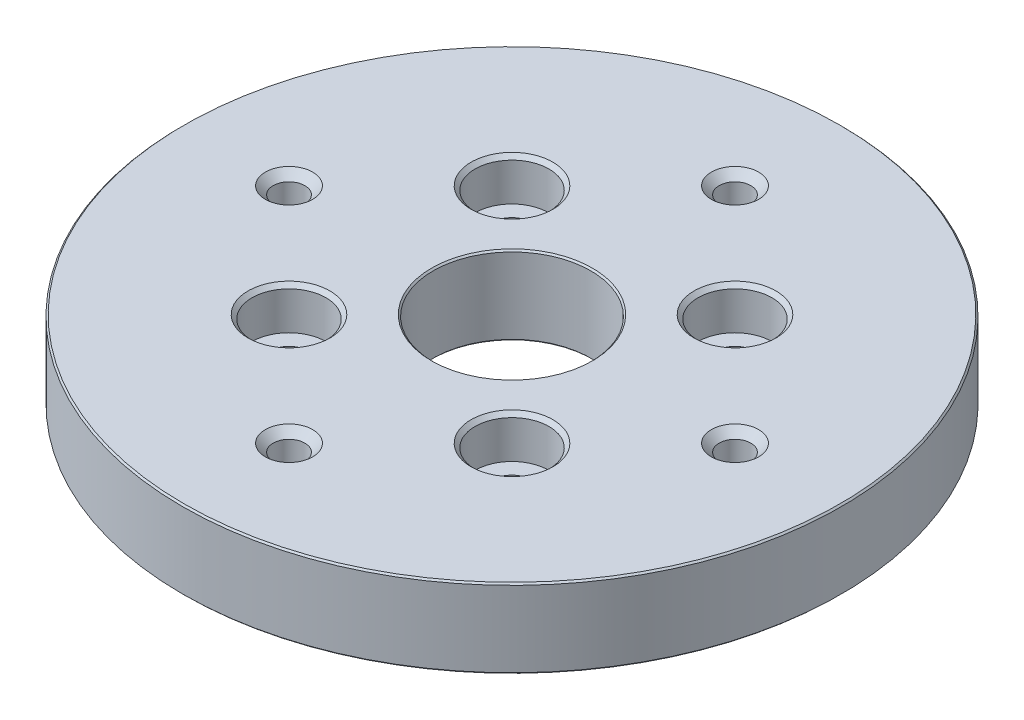
SolidWorks part; units mm, degrees
material "6061-T6 (SS)"
ref_plane "Front Plane" through (0, 0, 0) normal (0, 0, 1) x (1, 0, 0)
ref_plane "Top Plane" through (0, 0, 0) normal (0, 1, 0) x (1, 0, 0)
ref_plane "Right Plane" through (0, 0, 0) normal (1, 0, 0) x (0, 0, -1)
sketch "Sketch1" plane through (0, 0, 0) normal (0, 1, 0) x (1, 0, 0)
  line L0 (0, 35.921) -> (-35.921, 0) construction
  line L1 (-17.9605, 17.9605) -> (17.9605, 17.9605) construction
  line L2 (-17.9605, 17.9605) -> (-17.9605, -17.9605) construction
  line L3 (-17.9605, -17.9605) -> (17.9605, -17.9605) construction
  line L4 (17.9605, 17.9605) -> (17.9605, -17.9605) construction
  line L5 (-17.9605, 17.9605) -> (17.9605, -17.9605) construction
  line L6 (-17.9605, -17.9605) -> (17.9605, 17.9605) construction
  line L7 (0, 35.921) -> (35.921, 0) construction
  line L8 (-35.921, 0) -> (0, -35.921) construction
  line L9 (35.921, 0) -> (0, -35.921) construction
  line L10 (0, 35.921) -> (0, -35.921) construction
  line L11 (-35.921, 0) -> (35.921, 0) construction
  circle A0 centre (0, 0) radius 53.086
  circle A1 centre (0, 0) radius 12.7
  dimension "D1" = 106.172
  dimension "D2" = 25.4
  dimension "D3" = 50.8
  dimension "D4" = 50.8
extrude "Boss-Extrude1" add sketch "Sketch1" against normal blind 12.7
hole_wizard "1/4-20 Tapped Hole1" positions "Sketch3" profile "Sketch4" tap size "1/4-20" standard "ANSI Inch" end condition up to next
sketch "Sketch3" plane through (0, 0, 0) normal (0, 1, 0) x (1, 0, 0)
  point P0 (0, -35.921)
  point P3 (-35.921, 0)
  point P6 (0, 35.921)
  point P9 (35.921, 0)
sketch "Sketch4" plane through (0, 0, 35.921) normal (1, 0, 0) x (0, 0, 1)
  line L0 (0, 0) -> (0, 12.7)
  line L1 (0, 12.7) -> (3.81, 12.7)
  line L2 (2.5527, 11.4427) -> (2.5527, 1.2573)
  line L3 (2.5527, 1.2573) -> (3.81, 0)
  line L5 (3.81, 0) -> (0, 0)
  line L6 (-2.5527, 1.2573) -> (-3.81, 0) construction
  line L7 (3.81, 12.7) -> (2.5527, 11.4427)
  line L8 (-3.81, 12.7) -> (-2.5527, 11.4427) construction
  line L11 (0, -6.35) -> (0, 107.95) construction
  dimension "Thru Tap Drill Dia." = 5.1054
  dimension "Thru Tap Drill Depth" = 12.7
  dimension "Near C'Sink Dia." = 7.62
  dimension "Near C'Sink Angle" = 90
  dimension "Far C'Sink Dia." = 7.62
  dimension "Far C'Sink Angle" = 90
cosmetic thread "Hole Thread1" parameters "D2"=6.35
cosmetic thread "Hole Thread2" parameters "D2"=6.35
cosmetic thread "Hole Thread3" parameters "D2"=6.35
cosmetic thread "Hole Thread4" parameters "D2"=6.35
hole_wizard "CBORE for 1/4 Button Head Cap Screw1" positions "Sketch6" profile "Sketch5" counterbore size "1/4" standard "ANSI Inch" end condition up to next
sketch "Sketch6" plane through (0, 0, 0) normal (0, 1, 0) x (1, 0, 0)
  point P0 (-17.9605, -17.9605)
  point P3 (-17.9605, 17.9605)
  point P6 (17.9605, 17.9605)
  point P9 (17.9605, -17.9605)
sketch "Sketch5" plane through (-17.9605, 0, 17.9605) normal (1, 0, 0) x (0, 0, 1)
  line L0 (0, 0) -> (0, 12.7)
  line L1 (3.2639, 12.065) -> (3.8989, 12.7)
  line L2 (5.9538, 6.7564) -> (3.2639, 6.7564)
  line L3 (3.2639, 6.7564) -> (3.2639, 12.065)
  line L5 (5.9538, 6.7564) -> (5.9538, 0.635)
  line L6 (5.9538, 0.635) -> (6.5888, 0)
  line L7 (6.5888, 0) -> (0, 0)
  line L8 (-5.9538, 0.635) -> (-6.5888, 0) construction
  line L11 (0, -6.35) -> (0, 107.95) construction
  line L12 (3.8989, 12.7) -> (0, 12.7)
  line L13 (-3.2639, 12.065) -> (-3.8989, 12.7) construction
  dimension "Thru Hole Dia." = 6.5278
  dimension "Thru Hole Depth" = 12.7
  dimension "C'Bore Dia." = 11.9075
  dimension "C'Bore Depth" = 6.7564
  dimension "Near C'Sink Dia." = 13.1775
  dimension "Near C'Sink Angle" = 90
  dimension "Far C'Sink Dia." = 7.7978
  dimension "Far C'Sink Angle" = 90
chamfer "Chamfer1" distance 0.254 angle 45 4 edges at (0, -12.7, 53.086) (0, 0, 53.086) (0, -12.7, 12.7) (0, 0, 12.7)
